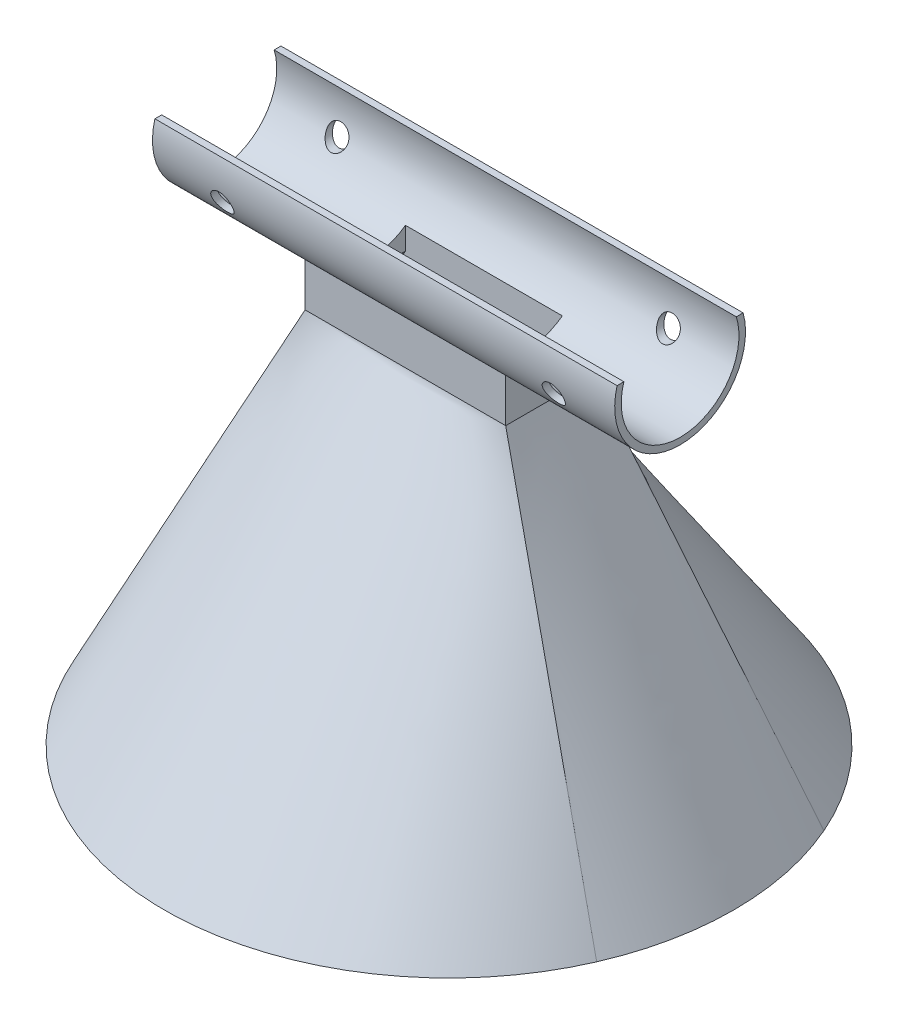
SolidWorks part; units mm, degrees
ref_plane "Front Plane" through (0, 0, 0) normal (0, 0, 1) x (1, 0, 0)
ref_plane "Top Plane" through (0, 0, 0) normal (0, 1, 0) x (1, 0, 0)
ref_plane "Right Plane" through (0, 0, 0) normal (1, 0, 0) x (0, 0, -1)
sketch "Sketch1" plane through (0, 0, 0) normal (0, 1, 0) x (1, 0, 0)
  circle A0 centre (0, 0) radius 65.3476
  dimension "D1" = 130.6952
ref_plane "Plane1" through (0, 80, 0) normal (0, 1, 0) x (1, 0, 0)
sketch "Sketch2" plane through (0, 80, 0) normal (0, 1, 0) x (1, 0, 0)
  line L1 (-23, 10) -> (23, 10)
  line L2 (-23, 10) -> (-23, -10)
  line L3 (-23, -10) -> (23, -10)
  line L4 (23, 10) -> (23, -10)
  line L5 (-23, 10) -> (23, -10) construction
  line L6 (-23, -10) -> (23, 10) construction
  point P0 (0, 0)
  dimension "D1" = 20
  dimension "D2" = 46
loft "Loft1" add profiles "Sketch2", "Sketch1"
sketch "Sketch3" plane through (0, 0, 0) normal (0, -1, 0) x (1, 0, 0)
  circle A0 centre (0, 0) radius 64
  dimension "D1" = 128
sketch "Sketch5" plane through (0, 80, 0) normal (0, 1, 0) x (1, 0, 0)
  line L0 (23, 10) -> (-23, 10) construction
  line L1 (-21, 8) -> (21, 8)
  line L2 (-21, 8) -> (-21, -8)
  line L3 (-21, -8) -> (21, -8)
  line L4 (21, 8) -> (21, -8)
  line L5 (-21, 8) -> (21, -8) construction
  line L6 (-21, -8) -> (21, 8) construction
  line L7 (23, -10) -> (23, 10) construction
  point P0 (0, 0)
  point P10 (23, 0)
  dimension "D1" = 2
  dimension "D2" = 2
loft "Cut-Loft3" cut profiles "Sketch5", "Sketch3"
sketch "Sketch12" plane through (0, 80, 0) normal (0, 1, 0) x (1, 0, 0)
  line L0 (-21, 8) -> (-21, -8) construction
  line L1 (21, 8) -> (-21, 8) construction
  line L2 (23, -10) -> (23, 10) construction
  line L3 (21, -8) -> (21, 8) construction
  line L4 (-21, -8) -> (21, -8) construction
  line L5 (-23, -10) -> (23, -10) construction
  line L6 (-23, 10) -> (-23, -10) construction
  line L7 (23, 10) -> (-23, 10) construction
  line L8 (-21, 8) -> (-21, -8)
  line L9 (21, 8) -> (-21, 8)
  line L10 (23, -10) -> (23, 10)
  line L11 (21, -8) -> (21, 8)
  line L12 (-21, -8) -> (21, -8)
  line L13 (-23, -10) -> (23, -10)
  line L14 (-23, 10) -> (-23, -10)
  line L15 (23, 10) -> (-23, 10)
extrude "Boss-Extrude5" add sketch "Sketch12" along normal blind 10
sketch "Sketch13" plane through (23, 0, 0) normal (1, 0, 0) x (0, 0, -1)
  line L0 (-12.8938, 105.1803) -> (-14.4568, 105.1803)
  line L1 (14.4568, 105.1803) -> (12.8938, 105.1803)
  arc A0 (-14.4568, 105.1803) -> (14.4568, 105.1803) centre (0, 101.1803) ccw
  arc A1 (-12.8938, 105.1803) -> (12.8938, 105.1803) centre (0, 101.1803) ccw
  dimension "D1" = 30
  dimension "D2" = 27
  dimension "D3" = 4
extrude "Boss-Extrude6" add sketch "Sketch13" against normal up to vertex (46 mm away) up to point (-23, 90, 10)
sketch "Sketch14" plane through (-23, 0, 0) normal (-1, 0, 0) x (0, 0, 1)
  line L0 (-12.8938, 105.1803) -> (12.8938, 105.1803)
  arc A0 (7.5664, 90) -> (12.8938, 105.1803) centre (0, 101.1803) ccw construction
  arc A1 (-12.8938, 105.1803) -> (12.8938, 105.1803) centre (0, 101.1803) ccw
  arc A2 (-12.8938, 105.1803) -> (-7.5664, 90) centre (0, 101.1803) ccw construction
extrude "Cut-Extrude5" cut sketch "Sketch14" against normal up to surface (46 mm away) up to face at (23, 94.769, 1)
sketch "Sketch15" plane through (0, 105.1803, 0) normal (0, 1, 0) x (1, 0, 0)
  line L1 (-18, 8) -> (18, 8)
  line L2 (-18, 8) -> (-18, -8)
  line L3 (-18, -8) -> (18, -8)
  line L4 (18, 8) -> (18, -8)
  line L5 (-18, 8) -> (18, -8) construction
  line L6 (-18, -8) -> (18, 8) construction
  point P0 (0, 0)
  dimension "D1" = 16
  dimension "D2" = 36
extrude "Cut-Extrude6" cut sketch "Sketch15" against normal blind 131
ref_plane "Plane4" through (0, 80, 0) normal (0, 1, 0) x (1, 0, 0)
sketch "Sketch20" plane through (0, 80, 0) normal (0, 1, 0) x (1, 0, 0)
  line L0 (-21, 8) -> (-18, 8) construction
  line L1 (-21, -8) -> (-21, 8) construction
  line L2 (-18, -8) -> (-18, 8) construction
  line L3 (-18, -8) -> (-21, -8) construction
  line L4 (-21, 8) -> (-18, 8)
  line L5 (-21, -8) -> (-21, 8)
  line L6 (-18, -8) -> (-18, 8)
  line L7 (-18, -8) -> (-21, -8)
  line L8 (21, -8) -> (18, -8) construction
  line L9 (21, 8) -> (21, -8) construction
  line L10 (18, 8) -> (21, 8) construction
  line L11 (18, 8) -> (18, -8) construction
  line L12 (21, -8) -> (18, -8)
  line L13 (21, 8) -> (21, -8)
  line L14 (18, 8) -> (21, 8)
  line L15 (18, 8) -> (18, -8)
extrude "Cut-Extrude7" cut sketch "Sketch20" along normal blind 26
sketch "Sketch21" plane through (21, 0, 0) normal (-1, 0, 0) x (0, 0, 1)
  line L0 (8, 90.3061) -> (8, 85.153)
  line L1 (8, 90.3061) -> (8, 80) construction
  line L2 (8, 85.153) -> (-8, 85.153)
  line L3 (-8, 90.3061) -> (-8, 80) construction
  line L4 (-8, 85.153) -> (-8, 90.3061)
  arc A0 (-8, 90.3061) -> (8, 90.3061) centre (0, 101.1803) ccw construction
  arc A1 (-8, 90.3061) -> (8, 90.3061) centre (0, 101.1803) ccw
extrude "Boss-Extrude8" add sketch "Sketch21" along normal blind 3
sketch "Sketch22" plane through (0, 0, -8) normal (0, 0, 1) x (1, 0, 0)
  line L0 (21, 85.153) -> (21, 80) construction
  line L1 (18, 85.153) -> (21, 85.153) construction
  line L2 (21, 85.153) -> (21, 80)
  line L3 (18, 85.153) -> (21, 85.153)
  line L4 (18, 85.153) -> (21, 80)
extrude "Boss-Extrude9" add sketch "Sketch22" along normal up to surface (16 mm away) up to face at (2.5, 86.4413, 8)
mirror "Mirror1" about plane through (0, 0, 0) normal (1, 0, 0) of "Boss-Extrude9", "Boss-Extrude8"
sketch "Sketch25" plane through (23, 0, 0) normal (1, 0, 0) x (0, 0, -1)
  line L0 (14.4568, 105.1803) -> (12.8938, 105.1803) construction
  line L1 (-12.8938, 105.1803) -> (-14.4568, 105.1803) construction
  line L2 (14.4568, 105.1803) -> (12.8938, 105.1803)
  line L3 (-12.8938, 105.1803) -> (-14.4568, 105.1803)
  arc A0 (10, 90) -> (14.4568, 105.1803) centre (0, 101.1803) ccw construction
  arc A1 (-14.4568, 105.1803) -> (-10, 90) centre (0, 101.1803) ccw construction
  arc A2 (-12.8938, 105.1803) -> (12.8938, 105.1803) centre (0, 101.1803) ccw construction
  arc A3 (10, 90) -> (14.4568, 105.1803) centre (0, 101.1803) ccw
  arc A4 (-14.4568, 105.1803) -> (-10, 90) centre (0, 101.1803) ccw
  arc A5 (-12.8938, 105.1803) -> (12.8938, 105.1803) centre (0, 101.1803) ccw
  arc A6 (-10, 90) -> (10, 90) centre (0, 101.1803) ccw
extrude "Boss-Extrude10" add sketch "Sketch25" along normal blind 30
sketch "Sketch26" plane through (-23, 0, 0) normal (-1, 0, 0) x (0, 0, 1)
  line L0 (12.8938, 105.1803) -> (14.4568, 105.1803) construction
  line L1 (-14.4568, 105.1803) -> (-12.8938, 105.1803) construction
  line L2 (12.8938, 105.1803) -> (14.4568, 105.1803)
  line L3 (-14.4568, 105.1803) -> (-12.8938, 105.1803)
  arc A0 (-14.4568, 105.1803) -> (-10, 90) centre (0, 101.1803) ccw construction
  arc A1 (10, 90) -> (14.4568, 105.1803) centre (0, 101.1803) ccw construction
  arc A2 (-12.8938, 105.1803) -> (12.8938, 105.1803) centre (0, 101.1803) ccw construction
  arc A3 (-14.4568, 105.1803) -> (-10, 90) centre (0, 101.1803) ccw
  arc A4 (10, 90) -> (14.4568, 105.1803) centre (0, 101.1803) ccw
  arc A5 (-12.8938, 105.1803) -> (12.8938, 105.1803) centre (0, 101.1803) ccw
  arc A6 (10, 90) -> (-10, 90) centre (0, 101.1803) cw
extrude "Boss-Extrude11" add sketch "Sketch26" along normal blind 30
sketch "Sketch27" plane through (0, 0, 10) normal (0, 0, 1) x (1, 0, 0)
  line L0 (0, 105.1803) -> (0, 80) construction
  line L1 (-53, 105.1803) -> (53, 105.1803) construction
  line L2 (-23, 80) -> (23, 80) construction
  line L3 (53, 95.6803) -> (-53, 96.4303) construction
  line L4 (53, 86.1803) -> (53, 105.1803) construction
  line L5 (-53, 105.1803) -> (-53, 87.6803) construction
  circle A0 centre (38, 95.7865) radius 2.5
  circle A1 centre (-38, 95.7865) radius 2.5
  point P14 (39.5497, 95.7755)
  dimension "D1" = 5
  dimension "D2" = 15
extrude "Cut-Extrude9" cut sketch "Sketch27" against normal through all and the other way through all
